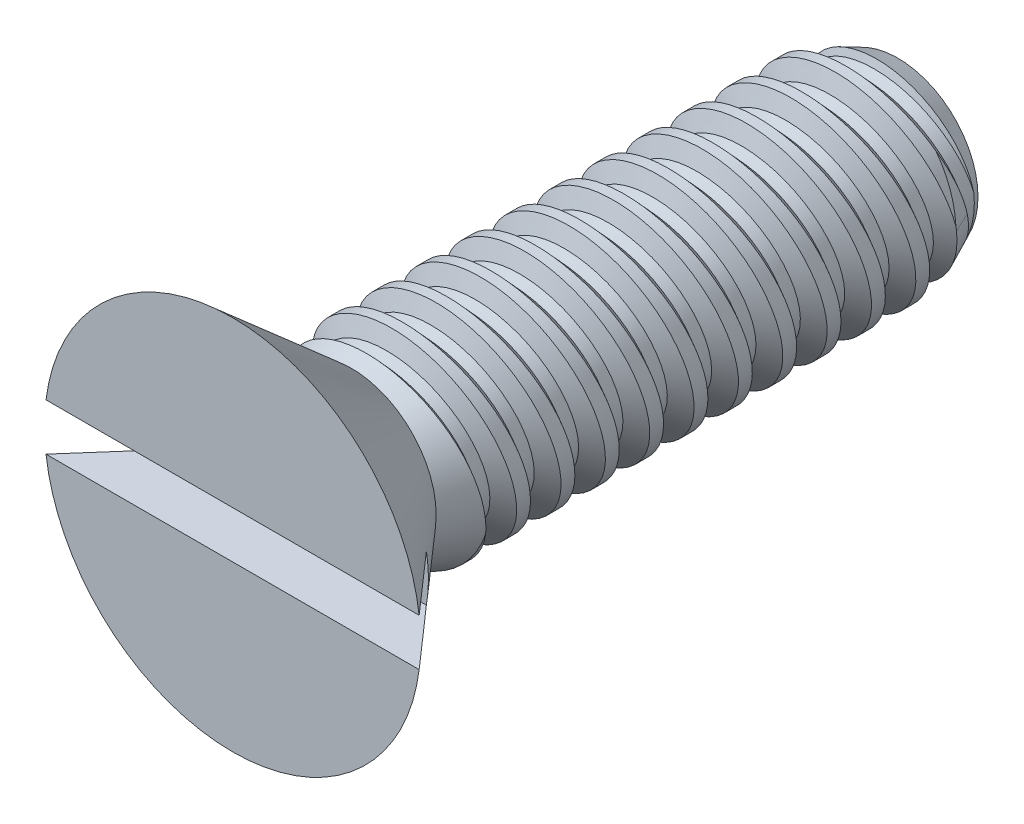
SolidWorks part; units mm, degrees
material "Brass"
ref_plane "Front" through (0, 0, 0) normal (0, 0, 1) x (1, 0, 0)
ref_plane "Top" through (0, 0, 0) normal (0, 1, 0) x (1, 0, 0)
ref_plane "Right" through (0, 0, 0) normal (1, 0, 0) x (0, 0, -1)
sketch "Sketch1" plane through (0, 0, 0) normal (0, 0, 1) x (1, 0, 0)
  circle A0 centre (0, 0) radius 2.6924
  dimension "Head Dia" = 5.3848
extrude "Extrude3" add sketch "Sketch1" along normal blind 1.7018
sketch "Sketch11" plane through (0, 0, 0) normal (1, 0, 0) x (0, 0, -1)
  line L0 (0.4414, 0) -> (-2.8754, 0) construction
  line L2 (0, 1.213) -> (-1.7018, 2.6924)
  line L3 (0, -2.6924) -> (0, 2.6924) construction
  line L5 (-1.7018, 2.6924) -> (0, 2.6924)
  line L7 (0, 2.6924) -> (0, 1.213)
  line L8 (0, 2.6924) -> (-1.7018, 2.6924) construction
  line L10 (-1.7018, 2.6924) -> (-1.7018, -2.6924) construction
  line L11 (0, -1.213) -> (-1.7018, -2.6924) construction
  dimension "D1" = 82
revolve "Cut-Revolve3" cut sketch "Sketch11" angle 360 about L0
sketch "Sketch4" plane through (0, 0, 0) normal (1, 0, 0) x (0, 0, -1)
  line L0 (0, 0) -> (7.8232, 0)
  line L2 (7.8232, -1.4224) -> (0, -1.4224) construction
  line L3 (7.8232, 0) -> (7.8232, 1.4224)
  line L4 (7.8232, 1.4224) -> (0, 1.4224)
  line L5 (-1.7018, 2.6924) -> (-1.7018, -2.6924) construction
  line L6 (0, 1.4224) -> (0, 0)
  line L7 (7.8232, 0) -> (10.3632, 0) construction
  dimension "D1" = 2.54
  dimension "Screw Dia" = 2.8448
  dimension "Screw Length" = 9.525
  dimension "Body Length" = 7.8232
revolve "Revolve1" add sketch "Sketch4" angle 360 about L7
sketch "Sketch5" plane through (0, 0, 0) normal (1, 0, 0) x (0, 0, -1)
  line L0 (0, 1.4224) -> (0.0775, 1.4397) construction
  line L1 (0, 1.4224) -> (0, -1.4224) construction
  line L2 (0.0775, 1.4397) -> (0.346, 1.1475)
  line L3 (0.346, 1.1475) -> (0.501, 1.1821)
  line L4 (0.501, 1.1821) -> (0.6197, 1.5607)
  line L5 (0.6197, 1.5607) -> (0.0775, 1.4397)
  line L6 (0.4235, 1.1648) -> (0.3486, 1.5002) construction
  line L7 (0, 1.4224) -> (0, 0) construction
  line L8 (0, -1.4224) -> (0.635, -1.4224) construction
  line L11 (0.635, -1.4224) -> (0, 1.4224) construction
  line L12 (7.8232, 1.4224) -> (0, 1.4224) construction
  line L13 (7.8232, -1.4224) -> (0, -1.4224) construction
  line L14 (0.366, 1.4224) -> (1.001, -1.4224) construction
  line L15 (0, -0.1526) -> (1.367, 0.1526) construction
  point P22 (0.6835, 0)
  dimension "D1" = 0.635
  dimension "Pitch" = 0.635
  dimension "D2" = 0.0794
  dimension "D3" = 0.1588
  dimension "D4" = 60
revolve "Cut-Revolve1" cut sketch "Sketch5" angle 360 about L15
sketch "Sketch13" plane through (0, 0, 0) normal (1, 0, 0) x (0, 0, -1)
  line L0 (7.8232, 1.1475) -> (7.2336, 1.4224)
  line L1 (7.8232, 0) -> (7.8232, 1.4224) construction
  line L2 (7.2336, 1.4224) -> (7.8232, 1.4224)
  line L3 (7.8232, 1.4224) -> (7.8232, 1.1475)
  line L4 (7.8232, 1.4224) -> (0, 1.4224) construction
  line L5 (0, 0) -> (7.2336, 0) construction
  line L6 (0, 0) -> (7.8232, 0) construction
  line L7 (7.2336, 1.4224) -> (7.2336, -1.4224) construction
  dimension "D1" = 25
  dimension "D2" = 2.8448
revolve "Cut-Revolve4" cut sketch "Sketch13" angle 360 about L5
sketch "Sketch16" plane through (0, 0, 0) normal (1, 0, 0) x (0, 0, -1)
  line L0 (0, 1.213) -> (0.5752, 1.4224)
  line L1 (0.5752, 1.4224) -> (0, 1.4224)
  line L2 (0, 1.4224) -> (0, 1.213)
  line L3 (0, 1.4224) -> (0, 0) construction
  line L4 (7.8232, 1.4224) -> (0, 1.4224) construction
  line L5 (0, 1.213) -> (-1.7018, 2.6924) construction
  line L6 (0, 1.213) -> (-1.7018, 2.6924) construction
  line L7 (0, 0) -> (7.8232, 0) construction
  line L8 (0, 0) -> (7.8232, 0) construction
  dimension "D1" = 20
revolve "Cut-Revolve5" cut sketch "Sketch16" angle 360 about L8
pattern_linear "LPattern2" count 12 spacing 0.635 along (0, 0, -1) of "Cut-Revolve1"
sketch "Sketch15" plane through (0, 0, 1.7018) normal (0, 0, 1) x (1, 0, 0)
  line L0 (-2.6924, 0.3365) -> (2.6924, -0.3365) construction
  line L1 (-2.6924, 0.3365) -> (2.6924, 0.3365)
  line L2 (-2.6924, 0.3365) -> (-2.6924, -0.3365)
  line L3 (-2.6924, -0.3365) -> (2.6924, -0.3365)
  line L4 (2.6924, 0.3365) -> (2.6924, -0.3365)
  circle A0 centre (0, 0) radius 2.6924 construction
  dimension "Slot Width" = 0.6731
extrude "Cut-Extrude5" cut sketch "Sketch15" against normal blind 0.8509
equation "\"D2@Sketch5\"=\"Pitch@Sketch5\"/8"
equation "\"D3@Sketch5\"=\"Pitch@Sketch5\"/4"
equation "\"D3@LPattern2\"=\"Pitch@Sketch5\""
equation "\"D1@LPattern2\"=\"Body Length@Sketch4\"/\"Pitch@Sketch5\""
equation "\"D1@Sketch5\"=\"Pitch@Sketch5\""
equation "\"Slot Width@Sketch15\"=\"Head Dia@Sketch1\"/8"
equation "\"Slot Depth@Cut-Extrude5\"=\"Head Ht@Extrude3\"/ 2"
